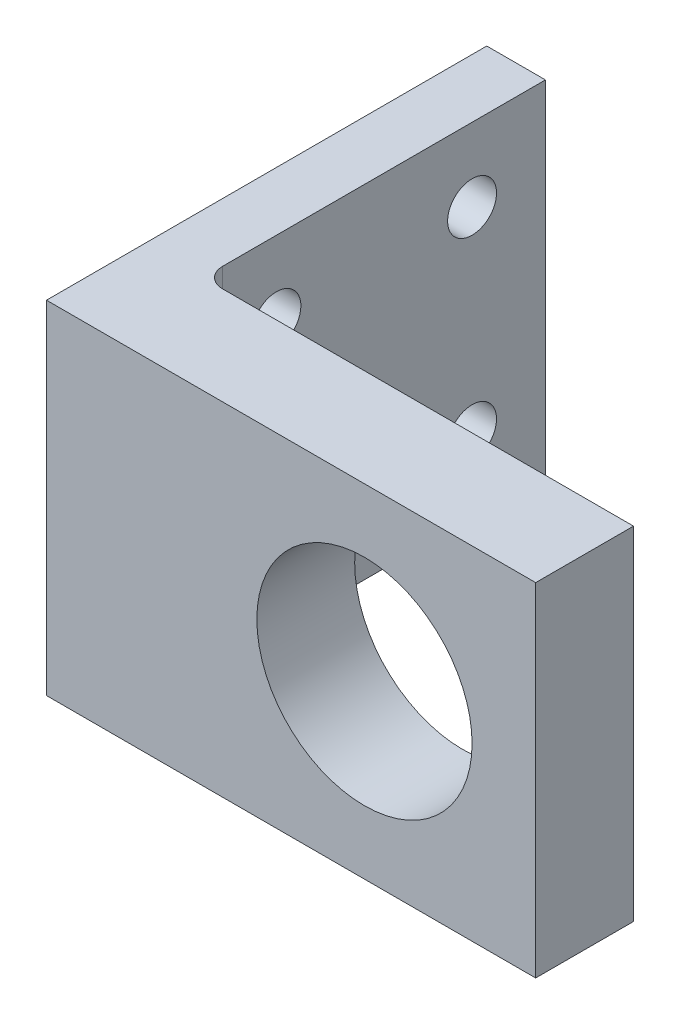
SolidWorks part; units mm, degrees
ref_plane "Piano frontale" through (0, 0, 0) normal (0, 0, 1) x (1, 0, 0)
ref_plane "Piano superiore" through (0, 0, 0) normal (0, 1, 0) x (1, 0, 0)
ref_plane "Piano destro" through (0, 0, 0) normal (1, 0, 0) x (0, 0, -1)
sketch "Sketch1" plane through (0, 0, 0) normal (0, 0, 1) x (1, 0, 0)
  line L0 (0, 17.5) -> (50, 17.5) construction
  line L1 (0, 0) -> (50, 0)
  line L2 (0, 0) -> (0, 35)
  line L3 (0, 35) -> (50, 35)
  line L4 (50, 0) -> (50, 35)
  line L5 (25, 35) -> (25, 0) construction
  line L6 (32.5, 17.5) -> (41.6924, 26.6924) construction
  line L7 (32.5, 17.5) -> (41.6924, 8.3076) construction
  line L8 (32.5, 17.5) -> (32.5, 0) construction
  line L9 (32.5, 17.5) -> (23.3076, 8.3076) construction
  line L10 (32.5, 17.5) -> (23.3076, 26.6924) construction
  circle A0 centre (32.5, 17.5) radius 11
  circle A6 centre (32.5, 17.5) radius 16 construction
  dimension "D2" = 22
  dimension "D7" = 17.5
  dimension "D9" = 32
  dimension "D1" = 50
  dimension "D3" = 17.5
  dimension "D5" = 45
  dimension "D8" = 35
extrude "Boss-Extrude3" add sketch "Sketch1" along normal blind 10
sketch "Sketch8" plane through (0, 0, 0) normal (0, 0, -1) x (-1, 0, 0)
  line L0 (-50, 35) -> (0, 35) construction
  line L3 (-6, 0) -> (0, 0)
  line L4 (0, 35) -> (0, 0)
  line L6 (0, 35) -> (0, 0) construction
  line L7 (-16.35, 17.5) -> (-32.5, 17.5) construction
  line L9 (0, 25) -> (0, 10)
  line L11 (-18.1947, 25) -> (-18.1947, 24.9954)
  line L12 (-6, 25) -> (-6, 35)
  line L13 (0, 35) -> (-6, 35)
  line L14 (0, 35) -> (0, 0)
  line L15 (0, 0) -> (-6, 0)
  line L16 (-6, 25) -> (-6, 10)
  line L17 (-6, 10) -> (-6, 0)
  dimension "D1" = 35
  dimension "D6" = 6
extrude "Boss-Extrude6" add sketch "Sketch8" along normal blind 35
sketch "Sketch9" plane through (6, 0, 0) normal (1, 0, 0) x (0, 0, -1)
  line L0 (0, 35) -> (35, 0) construction
  line L1 (35, 35) -> (0, 0) construction
  line L2 (17.5, 27.5) -> (17.5, 7.5) construction
  line L3 (7.5, 27.5) -> (27.5, 27.5) construction
  line L4 (7.5, 27.5) -> (7.5, 7.5) construction
  line L5 (7.5, 7.5) -> (27.5, 7.5) construction
  line L6 (27.5, 27.5) -> (27.5, 7.5) construction
  line L7 (27.5, 17.5) -> (7.5, 17.5) construction
  circle A0 centre (7.5, 27.5) radius 2.5
  circle A1 centre (27.5, 27.5) radius 2.5
  circle A2 centre (7.5, 7.5) radius 2.5
  circle A3 centre (27.5, 7.5) radius 2.5
  dimension "D2" = 5
  dimension "D1" = 20
extrude "Cut-Extrude1" cut sketch "Sketch9" against normal blind 10
fillet "Fillet1" radius 2 1 edges at (6, 17.5, 0)
